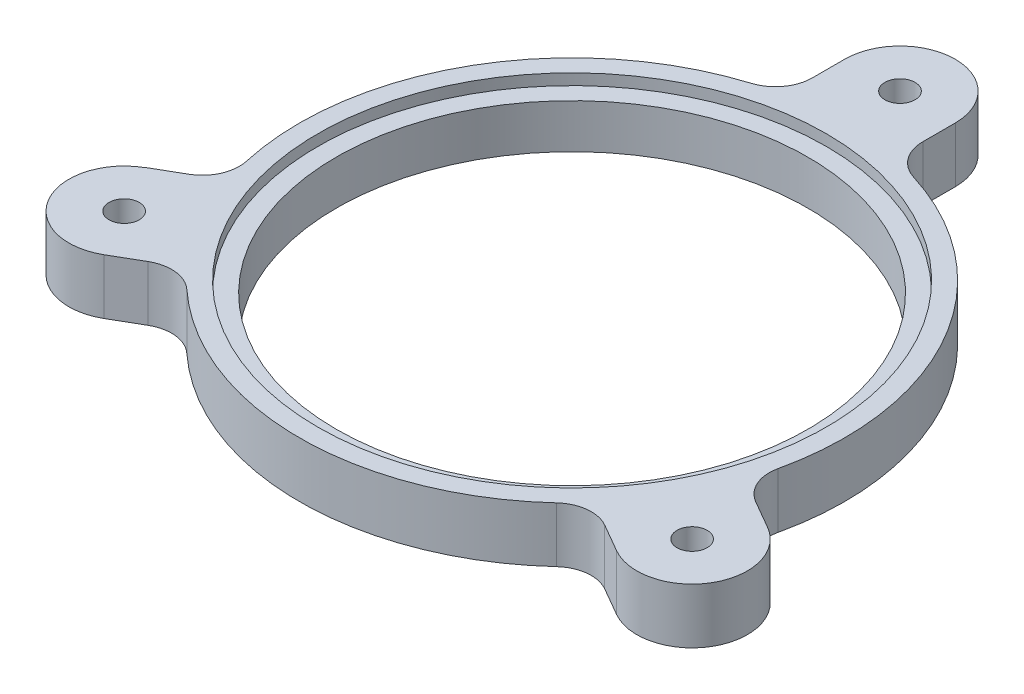
SolidWorks part; units mm, degrees
ref_plane "Front Plane" through (0, 0, 0) normal (0, 0, 1) x (1, 0, 0)
ref_plane "Top Plane" through (0, 0, 0) normal (0, 1, 0) x (1, 0, 0)
ref_plane "Right Plane" through (0, 0, 0) normal (1, 0, 0) x (0, 0, -1)
sketch "Sketch1" plane through (0, 0, 0) normal (0, 1, 0) x (1, 0, 0)
  line L0 (0, 0) -> (130.5675, -75.3832) construction
  line L1 (0, 98.2816) -> (0, 0) construction
  line L2 (0, 0) -> (-120.5871, -69.621) construction
  line L3 (84.5763, -31.5096) -> (76.9496, -27.1064)
  line L4 (-84.6083, -31.4541) -> (-84.5763, -31.5096)
  line L5 (69.5763, -57.4904) -> (61.9496, -53.0871)
  line L6 (46.2871, 89) -> (-60.4925, 89) construction
  line L7 (-69.5763, -57.4904) -> (-61.9496, -53.0871)
  line L9 (-84.6083, -31.4541) -> (-76.9644, -27.0408)
  line L10 (-15, 89) -> (-15, 80.1935)
  line L11 (15, 89) -> (15, 80.1935)
  circle A0 centre (0, 0) radius 69
  arc A1 (-22.0238, 70.6467) -> (-72.2067, -16.1924) centre (0, 0) ccw
  arc A3 (15, 89) -> (-15, 89) centre (0, 89) ccw
  arc A5 (-84.5763, -31.5096) -> (-69.5763, -57.4904) centre (-77.0763, -44.5) ccw
  arc A6 (69.5763, -57.4904) -> (84.5763, -31.5096) centre (77.0763, -44.5) ccw
  arc A7 (72.1937, -16.2502) -> (22.0238, 70.6467) centre (0, 0) ccw
  arc A8 (-50.1699, -54.3965) -> (50.1699, -54.3965) centre (0, 0) ccw
  circle A9 centre (-77.0763, -44.5) radius 4.1
  circle A10 centre (77.0763, -44.5) radius 4.1
  circle A11 centre (0, 89) radius 4.1
  arc A12 (-15, 80.1935) -> (-22.0238, 70.6467) centre (-25, 80.1935) cw
  arc A13 (15, 80.1935) -> (22.0238, 70.6467) centre (25, 80.1935) ccw
  arc A14 (76.9496, -27.1064) -> (72.1937, -16.2502) centre (81.9496, -18.4461) cw
  arc A15 (61.9496, -53.0871) -> (50.1699, -54.3965) centre (56.9496, -61.7474) ccw
  arc A16 (-61.9496, -53.0871) -> (-50.1699, -54.3965) centre (-56.9496, -61.7474) cw
  arc A17 (-76.9644, -27.0408) -> (-72.2067, -16.1924) centre (-81.9644, -18.3806) ccw
  point P27 (70.2555, -23.2415)
  point P38 (-55.2555, -49.2223)
  dimension "D1" = 10
  dimension "D2" = 10
  dimension "D3" = 10
  dimension "D4" = 10
  dimension "D5" = 10
  dimension "D6" = 10
extrude "Boss-Extrude1" add sketch "Sketch1" along normal blind 15
sketch "Sketch2" plane through (0, 0, 0) normal (0, 1, 0) x (1, 0, 0)
  circle A0 centre (0, 0) radius 69
  circle A1 centre (0, 0) radius 64
extrude "Boss-Extrude5" add sketch "Sketch2" along normal blind 12
